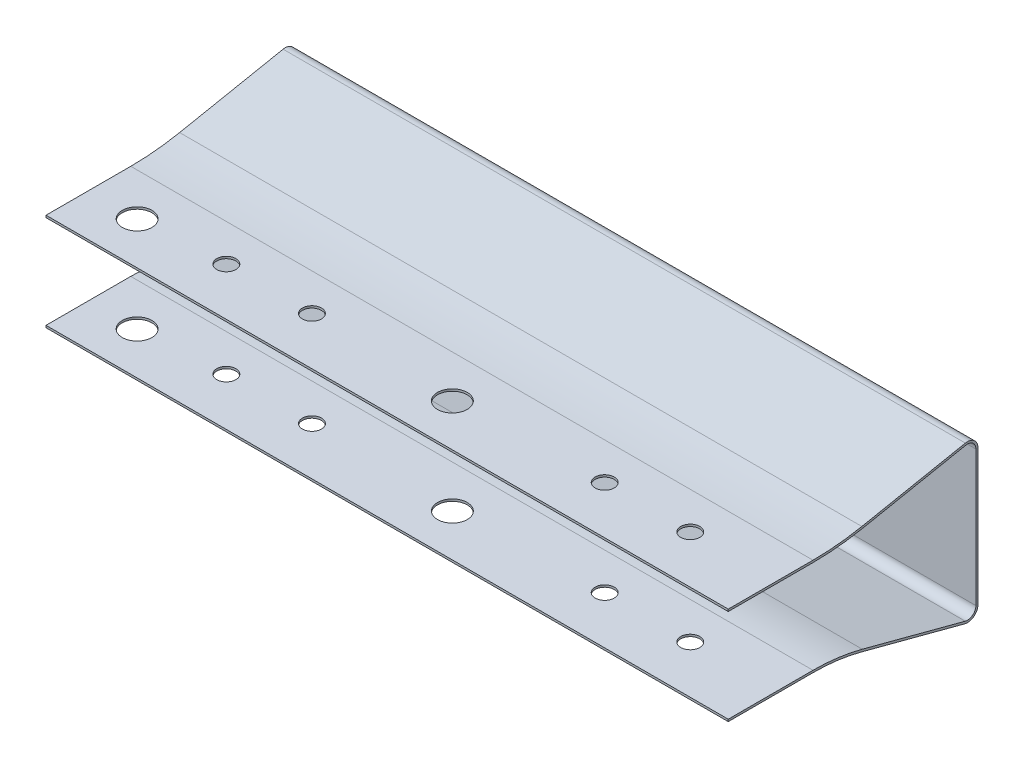
SolidWorks part; units mm, degrees
ref_plane "Front Plane" through (0, 0, 0) normal (0, 0, 1) x (1, 0, 0)
ref_plane "Top Plane" through (0, 0, 0) normal (0, 1, 0) x (1, 0, 0)
ref_plane "Right Plane" through (0, 0, 0) normal (1, 0, 0) x (0, 0, -1)
sketch "Sketch1" plane through (0, 0, 0) normal (1, 0, 0) x (0, 0, -1)
  line L0 (-14.22, 5) -> (-22.22, 5) construction
  line L1 (-24.22, 8) -> (-22.22, 8) construction
  line L2 (-24.22, 8) -> (-24.22, -8) construction
  line L3 (-24.22, -8) -> (-22.22, -8) construction
  line L4 (-14.22, 5) -> (-14.22, 3) construction
  line L5 (-24.22, 8) -> (-14.22, -5) construction
  line L6 (-24.22, -8) -> (-14.22, 5) construction
  line L7 (-22.22, 5) -> (-22.22, 8) construction
  line L8 (-14.22, 3) -> (-21.22, 3) construction
  line L9 (-21.22, 3) -> (-21.22, -3) construction
  line L10 (-21.22, -3) -> (-14.22, -3) construction
  line L11 (-14.22, -5) -> (-22.22, -5) construction
  line L12 (-22.22, -5) -> (-22.22, -8) construction
  line L13 (-14.22, -3) -> (-14.22, -5) construction
  line L14 (-24.22, 8) -> (-24.22, -8)
  line L15 (-10.8136, 6.5687) -> (-23.0262, 8.981)
  line L16 (-5, 5) -> (-5, -5) construction
  line L17 (-5, -5) -> (5, -5) construction
  line L18 (5, 5) -> (5, -5) construction
  line L19 (-5, 5) -> (5, -5) construction
  line L20 (-5, -5) -> (5, 5) construction
  line L21 (-5, 5) -> (5, 5) construction
  line L22 (-5, 5) -> (-5, 6) construction
  line L23 (-5, 6) -> (5, 6) construction
  line L24 (5, 5) -> (5, 6) construction
  line L25 (-10.8136, -5.7553) -> (-22.9645, -8.9668)
  line L26 (-5, -5) -> (5, -5)
  line L27 (-5, 6.25) -> (5, 6.25)
  line L28 (-5, 6) -> (5, 6)
  line L29 (-10.7651, 6.8139) -> (-22.9778, 9.2263)
  line L30 (-24.47, 8) -> (-24.47, -8)
  line L31 (-10.7497, -5.997) -> (-22.9006, -9.2085)
  line L32 (-5, -5.25) -> (5, -5.25)
  line L33 (5, 6.25) -> (5, 6)
  line L34 (5, -5) -> (5, -5.25)
  arc A0 (-24.22, -8) -> (-22.9645, -8.9668) centre (-23.22, -8) ccw
  arc A1 (-23.0262, 8.981) -> (-24.22, 8) centre (-23.22, 8) ccw
  arc A2 (-5, 6.25) -> (-10.7651, 6.8139) centre (-5, 36) cw
  arc A3 (-22.9778, 9.2263) -> (-24.47, 8) centre (-23.22, 8) ccw
  arc A4 (-24.47, -8) -> (-22.9006, -9.2085) centre (-23.22, -8) ccw
  arc A5 (-5, -5.25) -> (-10.7497, -5.997) centre (-5, -27.7512) ccw
  arc A6 (-5, -5) -> (-10.8136, -5.7553) centre (-5, -27.7512) ccw
  arc A7 (-5, 6) -> (-10.8136, 6.5687) centre (-5, 36) cw
  point P0 (-18.0662, 0)
  point P1 (0, 0)
  dimension "D13" = 30
  dimension "D17" = 1
  dimension "D1" = 16
  dimension "D2" = 10
  dimension "D3" = 2
  dimension "D4" = 2
  dimension "D5" = 2
  dimension "D6" = 3
  dimension "D7" = 6
  dimension "D8" = 3
  dimension "D9" = 10
  dimension "D10" = 10
  dimension "D11" = 16.22
  dimension "D12" = 1
  dimension "D14" = 0.25
extrude "Extrude1" add sketch "Sketch1" along normal mid plane 80.5
sketch "Sketch2" plane through (0, 0, 0) normal (0, 1, 0) x (1, 0, 0)
  line L0 (40.25, 5) -> (-40.25, 5) construction
  line L1 (-40.25, 5) -> (-40.25, -5) construction
  circle A0 centre (-34.5, 0) radius 1.75
  circle A1 centre (-24.62, -0.65) radius 1.125
  circle A2 centre (-14.52, -0.65) radius 1.125
  circle A3 centre (2.7, 0) radius 1.75
  circle A4 centre (20.02, -0.65) radius 1.125
  circle A5 centre (30.12, -0.65) radius 1.125
  dimension "D1" = 3.5
  dimension "D2" = 3.5
  dimension "D3" = 2.25
  dimension "D4" = 2.25
  dimension "D5" = 2.25
  dimension "D6" = 2.25
  dimension "D7" = 5
  dimension "D8" = 5.75
  dimension "D9" = 10.1
  dimension "D10" = 10.1
  dimension "D11" = 37.2
  dimension "D12" = 0.65
  dimension "D13" = 9.88
  dimension "D14" = 17.32
extrude "Cut-Extrude1" cut sketch "Sketch2" against normal through all and the other way through all
mirror "Mirror4" about plane through (0, 0, 0) normal (0, 0, 1) of bodies 102
delete or keep bodies "Body-Delete1" type delete bodies bodies 102
